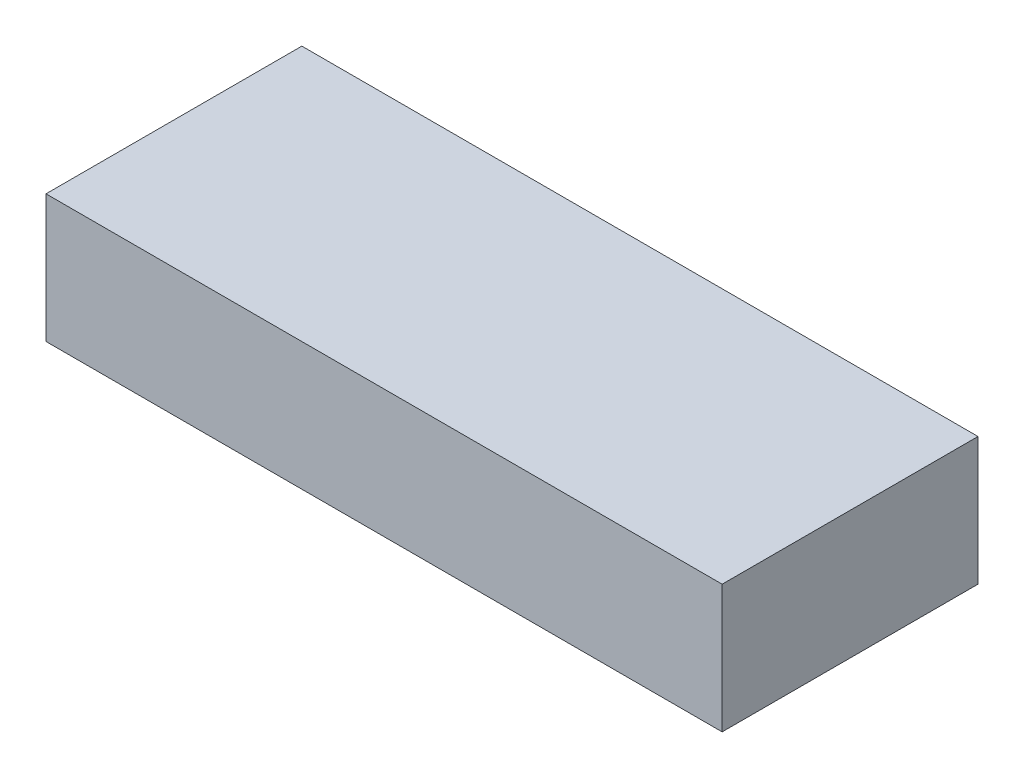
SolidWorks part; units mm, degrees
ref_plane "Front Plane" through (0, 0, 0) normal (0, 0, 1) x (1, 0, 0)
ref_plane "Top Plane" through (0, 0, 0) normal (0, 1, 0) x (1, 0, 0)
ref_plane "Right Plane" through (0, 0, 0) normal (1, 0, 0) x (0, 0, -1)
sketch "Sketch1" plane through (0, 0, 0) normal (0, 1, 0) x (1, 0, 0)
  line L1 (-185, 70) -> (185, 70)
  line L2 (-185, 70) -> (-185, -70)
  line L3 (-185, -70) -> (185, -70)
  line L4 (185, 70) -> (185, -70)
  line L5 (-185, 70) -> (185, -70) construction
  line L6 (-185, -70) -> (185, 70) construction
  point P0 (0, 0)
  dimension "D1" = 370
  dimension "D2" = 140
extrude "Boss-Extrude1" add sketch "Sketch1" along normal mid plane 70
